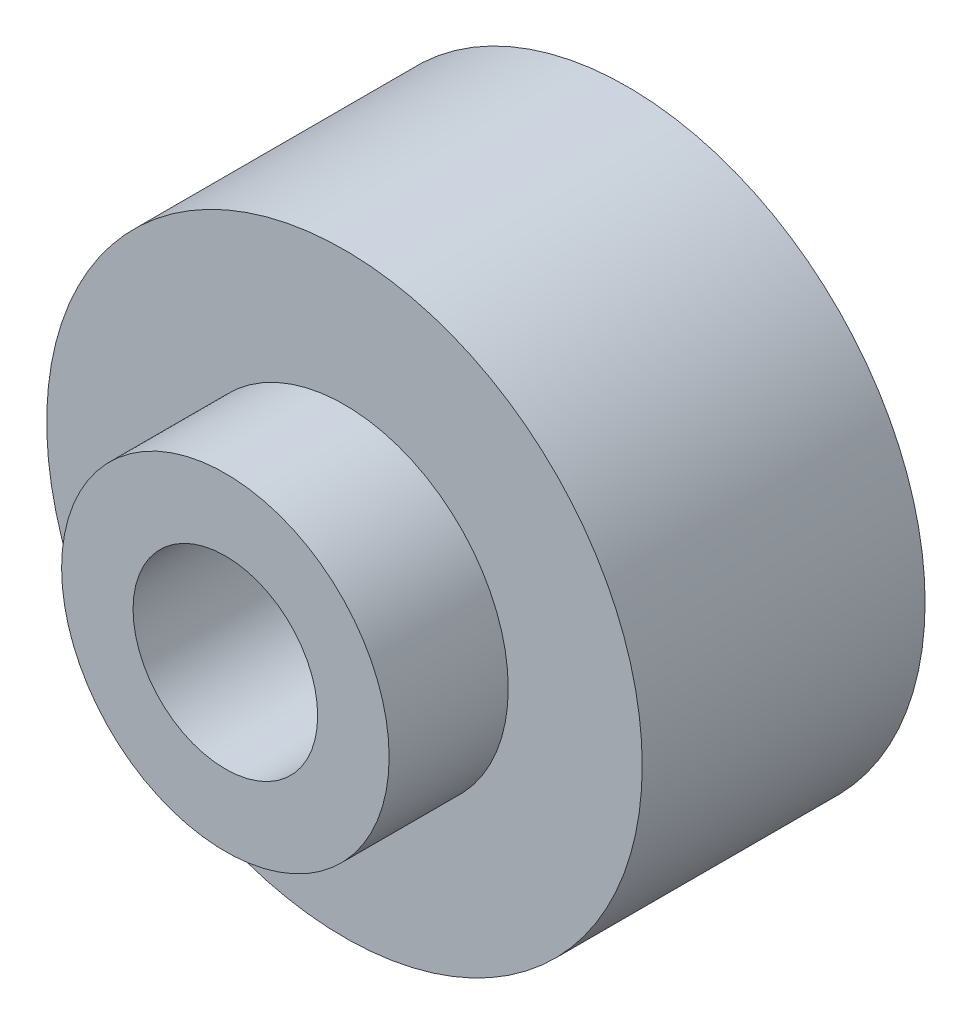
SolidWorks part; units mm, degrees
ref_plane "前视基准面" through (0, 0, 0) normal (0, 0, 1) x (1, 0, 0)
ref_plane "上视基准面" through (0, 0, 0) normal (0, 1, 0) x (1, 0, 0)
ref_plane "右视基准面" through (0, 0, 0) normal (1, 0, 0) x (0, 0, -1)
sketch "草图1" plane through (0, 0, 0) normal (0, 0, 1) x (1, 0, 0)
  circle A0 centre (0, 0) radius 5
  circle A1 centre (0, 0) radius 1.55
  dimension "D1" = 10
  dimension "D2" = 3.1
extrude "凸台-拉伸1" add sketch "草图1" along normal blind 4.75
sketch "草图2" plane through (0, 0, 4.75) normal (0, 0, 1) x (1, 0, 0)
  circle A0 centre (0, 0) radius 1.55
  circle A1 centre (0, 0) radius 2.75
  dimension "D1" = 5.5
extrude "凸台-拉伸2" add sketch "草图2" along normal blind 2
sketch "草图3" plane through (0, 0, 0) normal (0, 0, -1) x (-1, 0, 0)
  line L1 (1.7704, 2.9776) -> (-1.6935, 3.022)
  line L2 (-1.6935, 3.022) -> (-3.4638, 0.0444)
  line L3 (-3.4638, 0.0444) -> (-1.7704, -2.9776)
  line L4 (-1.7704, -2.9776) -> (1.6935, -3.022)
  line L5 (1.6935, -3.022) -> (3.4638, -0.0444)
  line L6 (3.4638, -0.0444) -> (1.7704, 2.9776)
  circle A0 centre (0, 0) radius 3 construction
  dimension "D1" = 6
extrude "切除-拉伸1" cut sketch "草图3" against normal blind 2.75
